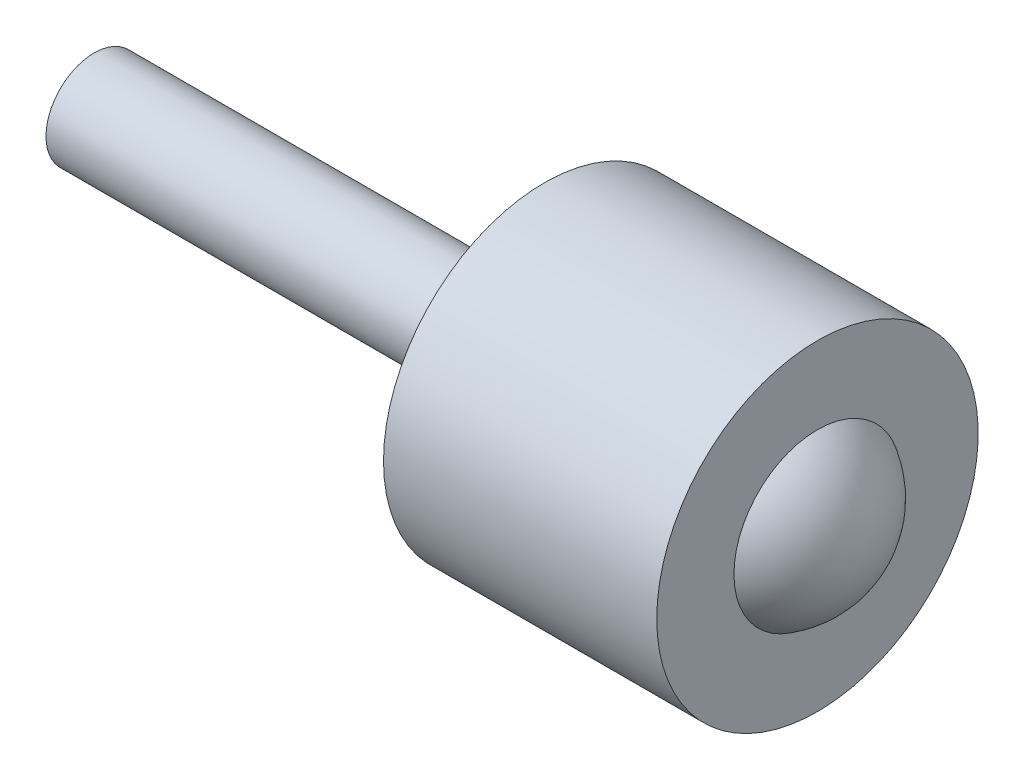
SolidWorks part; units mm, degrees
ref_plane "Front Plane" through (0, 0, 0) normal (0, 0, 1) x (1, 0, 0)
ref_plane "Top Plane" through (0, 0, 0) normal (0, 1, 0) x (1, 0, 0)
ref_plane "Right Plane" through (0, 0, 0) normal (1, 0, 0) x (0, 0, -1)
ref_axis "Axis1" through (-2.4, 0, 0) along (1, 0, 0)
sketch "Sketch1" plane through (0, 0, 0) normal (0, 0, 1) x (1, 0, 0)
  line L0 (0, 0) -> (48, 0)
  line L1 (0, 0) -> (0, 3)
  line L2 (0, 3) -> (28, 3)
  line L3 (28, 3) -> (28, 10)
  line L4 (28, 10) -> (45, 10)
  line L5 (45, 10) -> (45, 5.1962)
  arc A0 (48, 0) -> (45, 5.1962) centre (42, 0) ccw
  dimension "D7" = 6
  dimension "D1" = 17
  dimension "D2" = 28
  dimension "D3" = 3
  dimension "D4" = 10
  dimension "D5" = 3
revolve "Revolve1" add sketch "Sketch1" angle 360 about axis through (-2.4, 0, 0) along (1, 0, 0)
